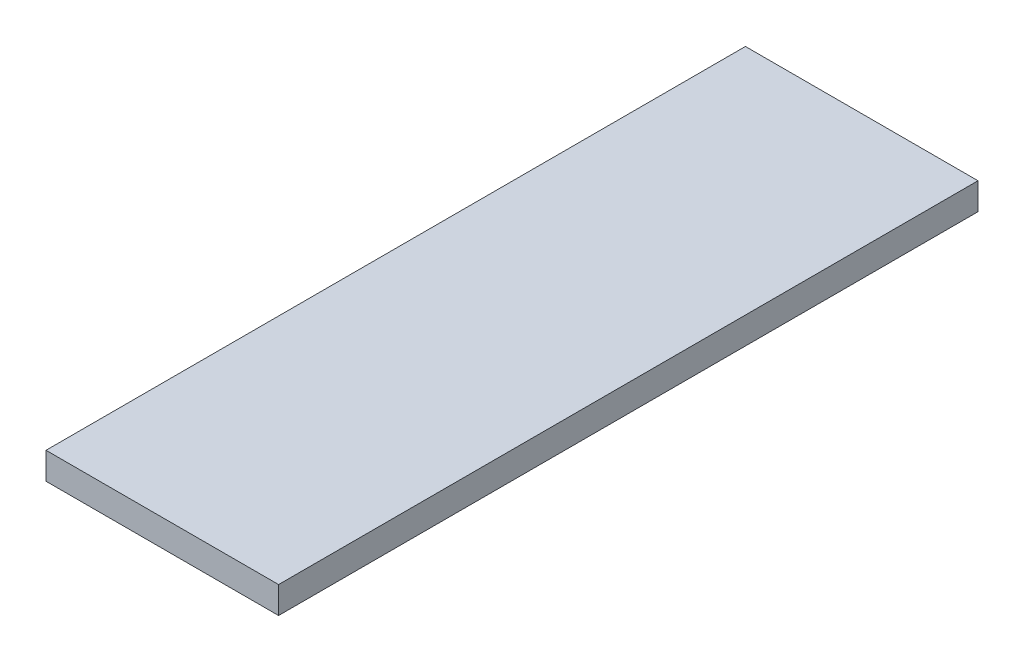
SolidWorks part; units mm, degrees
material "Balsa"
ref_plane "Alzado" through (0, 0, 0) normal (0, 0, 1) x (1, 0, 0)
ref_plane "Planta" through (0, 0, 0) normal (0, 1, 0) x (1, 0, 0)
ref_plane "Vista lateral" through (0, 0, 0) normal (1, 0, 0) x (0, 0, -1)
sketch "Croquis1" plane through (0, 0, 0) normal (0, 1, 0) x (1, 0, 0)
  line L2 (0, 0) -> (26, 0)
  line L3 (0, 0) -> (0, 78.19)
  line L4 (0, 78.19) -> (26, 78.19)
  line L5 (26, 0) -> (26, 78.19)
extrude "Saliente-Extruir1" add sketch "Croquis1" along normal blind 3
